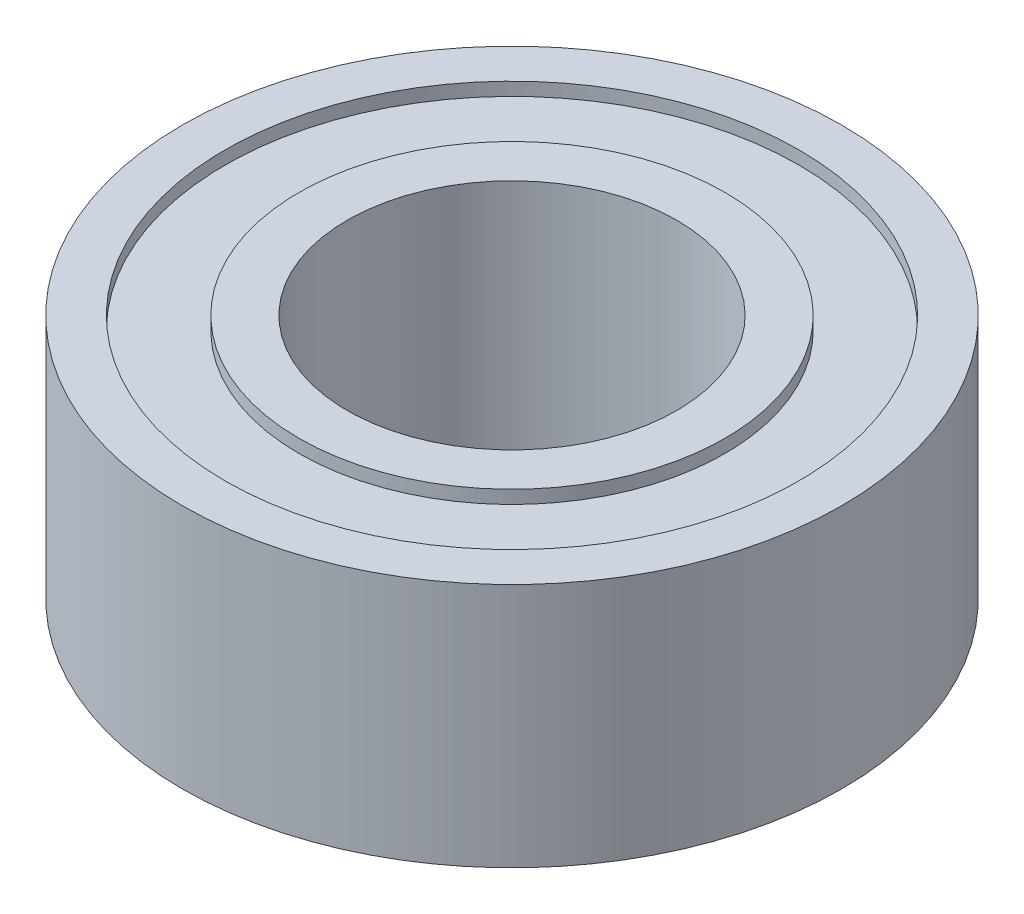
SolidWorks part; units mm, degrees
ref_plane "Front Plane" through (0, 0, 0) normal (0, 0, 1) x (1, 0, 0)
ref_plane "Top Plane" through (0, 0, 0) normal (0, 1, 0) x (1, 0, 0)
ref_plane "Right Plane" through (0, 0, 0) normal (1, 0, 0) x (0, 0, -1)
sketch "Sketch1" plane through (0, 0, 0) normal (0, 0, 1) x (1, 0, 0)
  line L0 (4.1021, 4.7244) -> (3.175, 4.7244)
  line L1 (3.175, 4.7244) -> (3.175, 0)
  line L2 (3.175, 0) -> (4.1021, 0)
  line L3 (4.1021, 0) -> (4.1021, 0.254)
  line L4 (4.1021, 0.254) -> (5.5245, 0.254)
  line L5 (5.5245, 0.254) -> (5.5245, 0)
  line L6 (5.5245, 0) -> (6.35, 0)
  line L7 (6.35, 0) -> (6.35, 4.7244)
  line L8 (6.35, 4.7244) -> (5.5245, 4.7244)
  line L9 (5.5245, 4.7244) -> (5.5245, 4.4704)
  line L10 (5.5245, 4.4704) -> (4.1021, 4.4704)
  line L11 (4.1021, 4.4704) -> (4.1021, 4.7244)
  line L12 (0, 4.7244) -> (0, 0) construction
revolve "Revolve1" add sketch "Sketch1" angle 360 about L12
